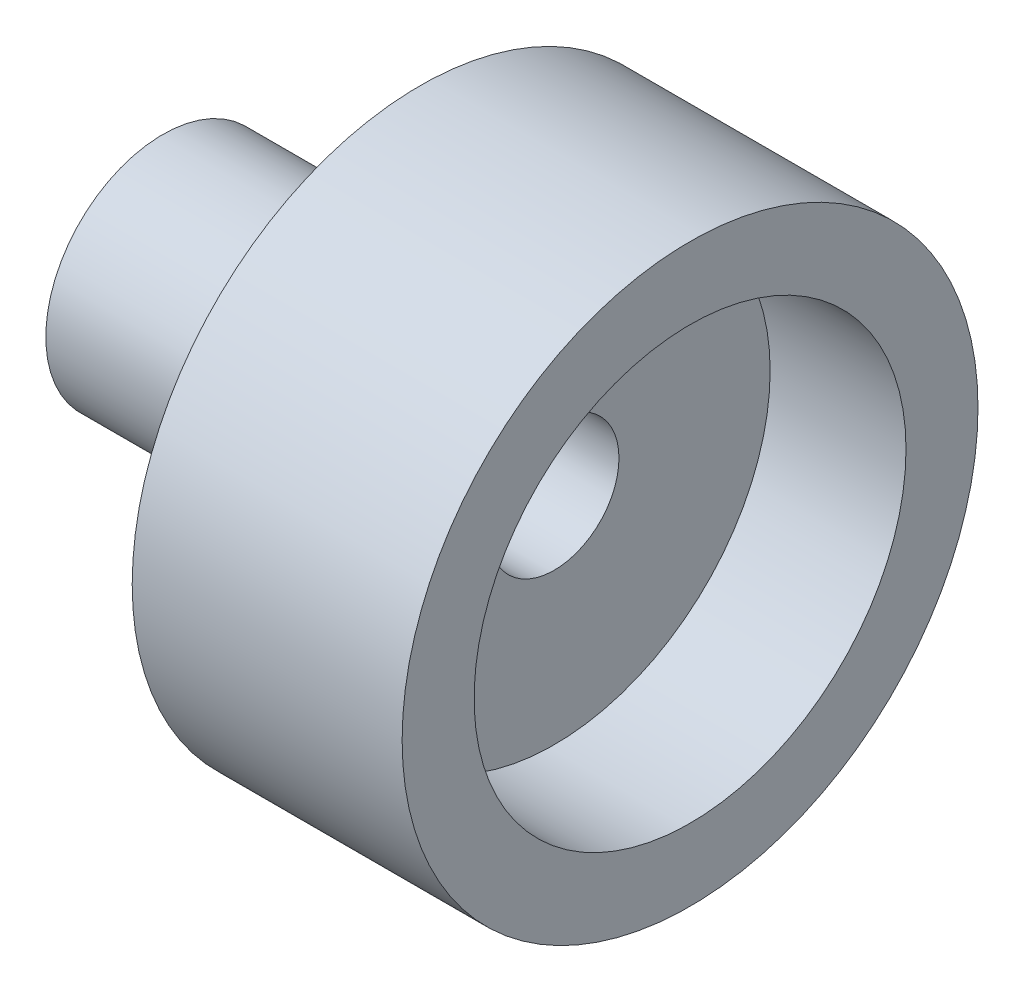
SolidWorks part; units mm, degrees
material "ABS PC"
ref_plane "Front Plane" through (0, 0, 0) normal (0, 0, 1) x (1, 0, 0)
ref_plane "Top Plane" through (0, 0, 0) normal (0, 1, 0) x (1, 0, 0)
ref_plane "Right Plane" through (0, 0, 0) normal (1, 0, 0) x (0, 0, -1)
sketch "Sketch2" plane through (0, 0, 0) normal (1, 0, 0) x (0, 0, -1)
  circle A0 centre (0, 0) radius 8
  circle A1 centre (0, 0) radius 3.25
  dimension "D1" = 16
extrude "Boss-Extrude1" add sketch "Sketch2" along normal blind 7.5
sketch "Sketch3" plane through (7.5, 0, 0) normal (1, 0, 0) x (0, 0, -1)
  circle A0 centre (0, 0) radius 6
extrude "Cut-Extrude1" cut sketch "Sketch3" against normal blind 3.775
sketch "Sketch4" plane through (3.725, 0, 0) normal (1, 0, 0) x (0, 0, -1)
  circle A0 centre (0, 0) radius 1.8
  circle A1 centre (0, 0) radius 3.25
extrude "Boss-Extrude2" add sketch "Sketch4" against normal blind 10.875
sketch "Sketch5" plane through (7.5, 0, 0) normal (1, 0, 0) x (0, 0, -1)
  line L1 (1.8, 0) -> (-1.8, 0)
  line L2 (1.8, 0) -> (1.8, 10.1496)
  line L3 (1.8, 10.1496) -> (-1.8, 10.1496)
  line L4 (-1.8, 0) -> (-1.8, 10.1496)
  dimension "D1" = 3.6
  dimension "D2" = 1.8
extrude "Cut-Extrude2" [suppressed] cut sketch "Sketch5" against normal through all
